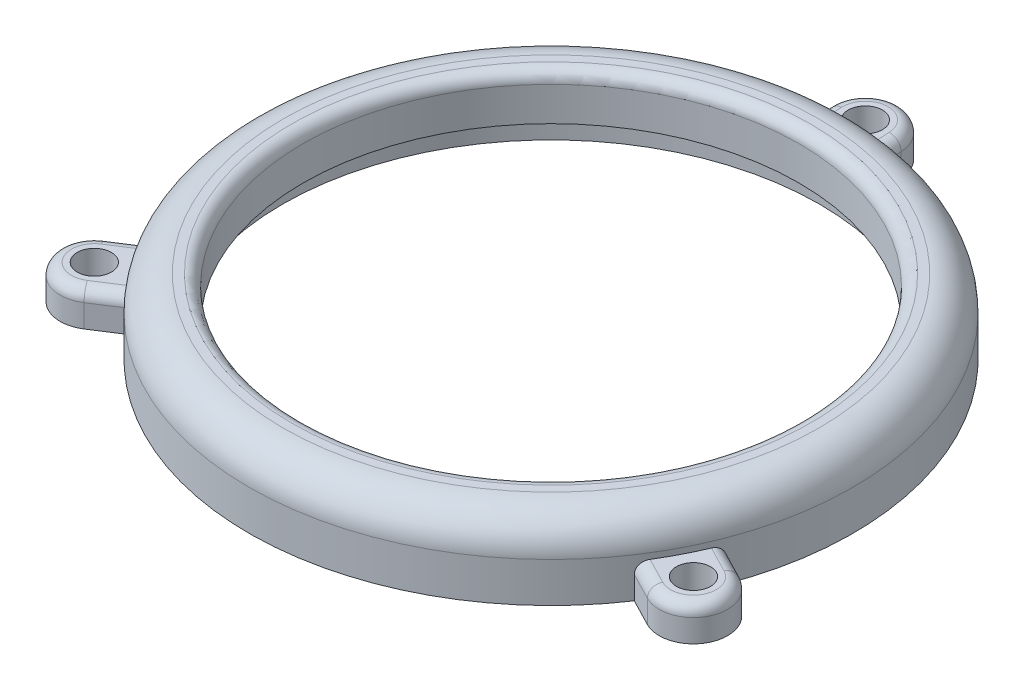
SolidWorks part; units mm, degrees
ref_plane "Front Plane" through (0, 0, 0) normal (0, 0, 1) x (1, 0, 0)
ref_plane "Top Plane" through (0, 0, 0) normal (0, 1, 0) x (1, 0, 0)
ref_plane "Right Plane" through (0, 0, 0) normal (1, 0, 0) x (0, 0, -1)
sketch "Sketch1" plane through (0, 0, 0) normal (0, 1, 0) x (1, 0, 0)
  circle A0 centre (0, 0) radius 21.75
  circle A1 centre (0, 0) radius 26.5
  dimension "D1" = 43.5
  dimension "D2" = 53
extrude "Boss-Extrude1" add sketch "Sketch1" along normal blind 6.5
fillet "Fillet1" radius 3 1 edges at (0, 6.5, 26.5)
sketch "Sketch2" plane through (0, 0, 0) normal (0, -1, 0) x (1, 0, 0)
  circle A0 centre (0, 0) radius 21.75
  circle A1 centre (0, 0) radius 23.55
  circle A2 centre (0, 0) radius 21.75 construction
  dimension "D1" = 47.1
extrude "Cut-Extrude1" cut sketch "Sketch2" against normal blind 2.51
sketch "Sketch3" plane through (0, 0, 0) normal (0, -1, 0) x (1, 0, 0)
  line L0 (-20.524, 16.7636) -> (-23.769, 11.7168)
  line L1 (-23.769, 11.7168) -> (-26.0151, 13.1611)
  line L2 (-20.524, 16.7636) -> (-22.7701, 18.2078)
  arc A1 (-22.7701, 18.2078) -> (-26.0151, 13.1611) centre (-24.3926, 15.6844) ccw
  circle A2 centre (0, 0) radius 26.5 construction
  circle A3 centre (-24.3926, 15.6844) radius 1.5
  dimension "D1" = 3
  dimension "D2" = 3
  dimension "D3" = 29
extrude "Boss-Extrude2" add sketch "Sketch3" against normal blind 3
pattern_circular "CirPattern1" count 3 every 120 about axis through (0, 0, 0) along (0, 1, 0) of "Boss-Extrude2"
fillet "Fillet2" radius 1 1 edges at (0, 6.5, 21.75)
fillet "Fillet4" radius 1 9 edges at (23.2185, 3, 15.3377) (25.9666, 3, 10.004) (28.4462, 3, 14.6564) (-4.3195, 3, -27.4897) (-1.5303, 3, -31.9634) (1.6736, 3, -27.7766) (-24.8921, 3, 12.4389) (-26.916, 3, 17.307) (-21.647, 3, 17.4857)
